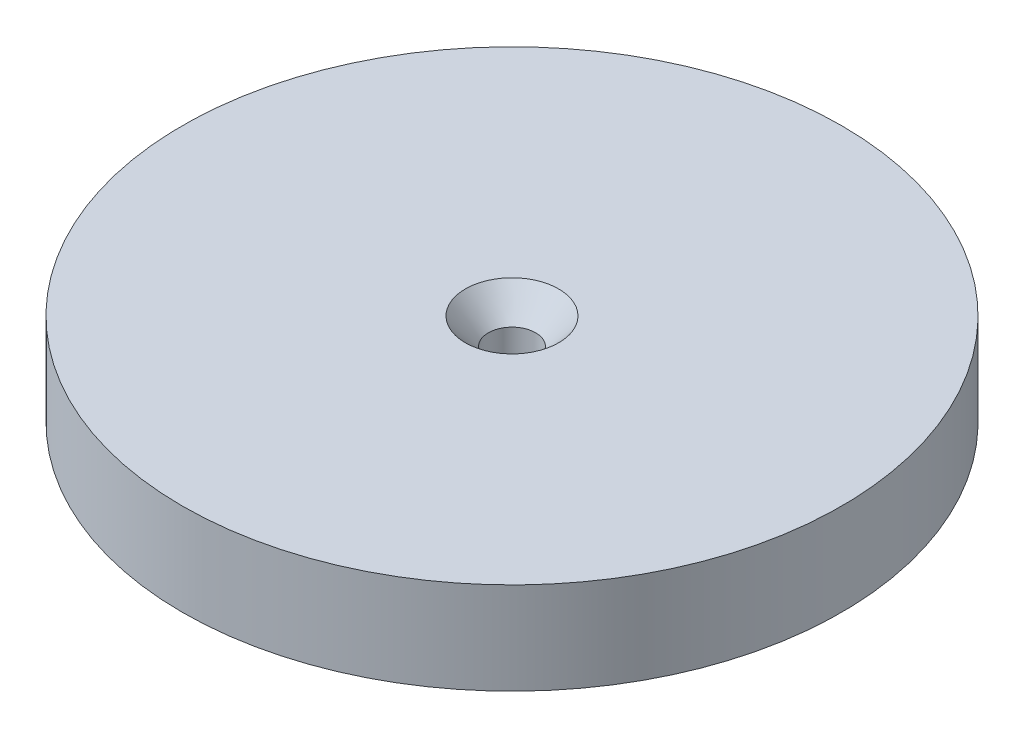
SolidWorks part; units mm, degrees
ref_plane "Front Plane" through (0, 0, 0) normal (0, 0, 1) x (1, 0, 0)
ref_plane "Top Plane" through (0, 0, 0) normal (0, 1, 0) x (1, 0, 0)
ref_plane "Right Plane" through (0, 0, 0) normal (1, 0, 0) x (0, 0, -1)
sketch "Sketch1" plane through (0, 0, 0) normal (0, 1, 0) x (1, 0, 0)
  circle A0 centre (0, 0) radius 20.066 construction
  circle A1 centre (0, 0) radius 45.466
  dimension "D1" = 25.4
extrude "Boss-Extrude1" add sketch "Sketch1" along normal blind 25.4
sketch "Sketch3" plane through (0, 0, 0) normal (0, -1, 0) x (1, 0, 0)
  circle A0 centre (0, 0) radius 20.32
extrude "Cut-Extrude1" cut sketch "Sketch3" against normal blind 12.7
sketch "Sketch4" plane through (0, 0, 0) normal (0, -1, 0) x (1, 0, 0)
  line L0 (0, 0) -> (0, 31.75) construction
  circle A0 centre (0, 31.75) radius 1.524
hole_wizard "CSK for 1/4 Flat Head Machine Screw1" positions "Sketch6" profile "Sketch7" countersink size "1/4" standard "ANSI Inch"
sketch "Sketch6" plane through (0, 25.4, 0) normal (0, 1, 0) x (1, 0, 0)
  point P0 (0, 0)
sketch "Sketch7" plane through (0, 25.4, 0) normal (1, 0, 0) x (0, 0, 1)
  line L0 (0, 0) -> (0, 27.3611)
  line L1 (0, 27.3611) -> (3.2639, 25.4)
  line L2 (3.2639, 25.4) -> (3.2639, 3.6524)
  line L3 (3.2639, 3.6524) -> (6.4389, 0)
  line L5 (6.4389, 0) -> (0, 0)
  line L6 (-3.2639, 3.6524) -> (-6.4389, 0) construction
  line L10 (0, 27.3611) -> (-3.2639, 25.4) construction
  line L11 (0, -6.35) -> (0, 107.95) construction
  dimension "Hole Dia." = 6.5278
  dimension "Hole Depth" = 25.4
  dimension "Near C'Sink Dia." = 12.8778
  dimension "Near C'Sink Angle" = 82
  dimension "Drill Angle" = 118
sketch "Sketch9" plane through (0, 0, 0) normal (0, -1, 0) x (1, 0, 0)
  circle A0 centre (0, 0) radius 53.0319
extrude "Cut-Extrude3" cut sketch "Sketch9" against normal blind 12.7
